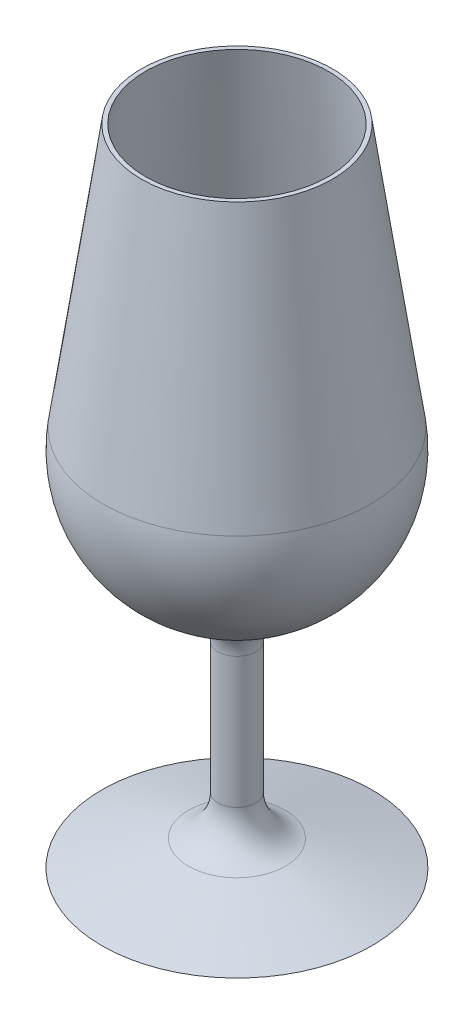
SolidWorks part; units mm, degrees
ref_plane "Front Plane" through (0, 0, 0) normal (0, 0, 1) x (1, 0, 0)
ref_plane "Top Plane" through (0, 0, 0) normal (0, 1, 0) x (1, 0, 0)
ref_plane "Right Plane" through (0, 0, 0) normal (1, 0, 0) x (0, 0, -1)
sketch "Sketch2" plane through (0, 0, 0) normal (0, 0, 1) x (1, 0, 0)
  line L0 (0, 117.9087) -> (0, -41.2278) construction
  line L1 (0, -37.0913) -> (32.5, -37.0913)
  line L2 (32.5, -37.0913) -> (11.6665, -30.9357)
  line L3 (4.5, -21.3456) -> (4.5, 10.1457)
  line L4 (21.9895, 117.9087) -> (23, 117.9087)
  line L5 (23, 117.9087) -> (32.1631, 54.7629)
  line L6 (22.1346, 116.9087) -> (31.1735, 54.6193) construction
  line L7 (21.9895, 117.9087) -> (31.1735, 54.6193)
  line L8 (0, 18.5957) -> (0, -37.0913)
  line L11 (0, 117.9087) -> (23, 117.9087) construction
  line L13 (1, -36.0913) -> (1, 116.9087) construction
  line L14 (0, -37.0913) -> (0, 117.9087) construction
  line L15 (1, 116.9087) -> (22.1346, 116.9087) construction
  line L16 (1, -36.0913) -> (25.5864, -36.0913) construction
  line L17 (25.5864, -36.0913) -> (11.3831, -31.8947) construction
  line L18 (3.5, -21.3456) -> (3.5, 10.1457) construction
  arc A0 (11.0882, 19.5457) -> (32.1631, 54.7629) centre (0, 50.0957) ccw
  arc A1 (11.0882, 19.5457) -> (4.5, 10.1457) centre (14.5, 10.1457) ccw
  arc A2 (4.5, -21.3456) -> (11.6665, -30.9357) centre (14.5, -21.3456) ccw
  arc A3 (0, 18.5957) -> (31.1735, 54.6193) centre (0, 50.0957) ccw
  arc A6 (10.7471, 20.4857) -> (31.1735, 54.6193) centre (0, 50.0957) ccw construction
  arc A7 (10.7471, 20.4857) -> (3.5, 10.1457) centre (14.5, 10.1457) ccw construction
  arc A8 (3.5, -21.3456) -> (11.3831, -31.8947) centre (14.5, -21.3456) ccw construction
  point P12 (4.5, 17.9087)
  dimension "D7" = 10
  dimension "D6" = 32.5
  dimension "D8" = 10
  dimension "D1" = 32.5
  dimension "D2" = 55
  dimension "D3" = 4.5
  dimension "D4" = 23
  dimension "D5" = 100
  dimension "D9" = 1
revolve "Revolve1" add sketch "Sketch2" angle 360 about L0
